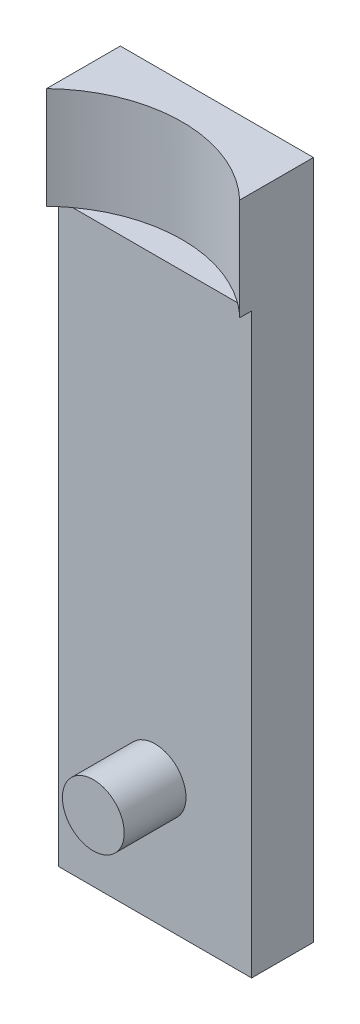
SolidWorks part; units mm, degrees
ref_plane "Front Plane" through (0, 0, 0) normal (0, 0, 1) x (1, 0, 0)
ref_plane "Top Plane" through (0, 0, 0) normal (0, 1, 0) x (1, 0, 0)
ref_plane "Right Plane" through (0, 0, 0) normal (1, 0, 0) x (0, 0, -1)
sketch "Sketch1" plane through (0, 0, 0) normal (0, 0, 1) x (1, 0, 0)
  line L1 (-31.25, 110) -> (31.25, 110)
  line L2 (-31.25, 110) -> (-31.25, -110)
  line L3 (-31.25, -110) -> (31.25, -110)
  line L4 (31.25, 110) -> (31.25, -110)
  line L5 (-31.25, 110) -> (31.25, -110) construction
  line L6 (-31.25, -110) -> (31.25, 110) construction
  point P0 (0, 0)
  dimension "D1" = 220
  dimension "D2" = 62.5
extrude "Boss-Extrude1" add sketch "Sketch1" along normal blind 20
sketch "Sketch2" plane through (0, 0, 20) normal (0, 0, 1) x (1, 0, 0)
  line L1 (-31.25, 110) -> (31.25, 110)
  line L2 (-31.25, 110) -> (-31.25, 77)
  line L3 (-31.25, 77) -> (31.25, 77)
  line L4 (31.25, 110) -> (31.25, 77)
  line L5 (31.25, -110) -> (31.25, 110) construction
  dimension "D1" = 33
  dimension "D2" = 62.5
extrude "Boss-Extrude2" add sketch "Sketch2" along normal blind 5
sketch "Sketch3" plane through (0, 0, 20) normal (0, 0, 1) x (1, 0, 0)
  line L2 (-31.25, -110) -> (31.25, -110) construction
  circle A1 centre (0, -70) radius 10
  dimension "D1" = 40
  dimension "D2" = 20
extrude "Cut-Extrude1" cut sketch "Sketch3" against normal through all
sketch "Sketch4" plane through (0, 110, 0) normal (0, 1, 0) x (1, 0, 0)
  line L0 (31.25, -25) -> (0, -56.25)
  line L1 (31.25, -25) -> (-31.25, -25)
  line L2 (-31.25, -25) -> (0, -56.25)
  line L3 (30.0734, -25) -> (-32.3796, -25)
  circle A0 centre (0, -56.25) radius 45
  line M6 (-31.25, 0) -> (-31.25, -25)
  line M7 (-31.25, -25) -> (31.25, -25)
  line M8 (31.25, -25) -> (31.25, 0)
  dimension "D2" = 90
  dimension "D1" = 45
  dimension "45" = 45
extrude "Cut-Extrude2" cut sketch "Sketch4" against normal blind 33 contours A0 L1 M8 M6 M7
sketch "Sketch5" plane through (0, 0, 20) normal (0, 0, 1) x (1, 0, 0)
  circle A0 centre (0, -70) radius 10
  dimension "D1" = 20
extrude "Boss-Extrude3" add sketch "Sketch5" along normal blind 20 separate body
sketch "Sketch6" plane through (0, 0, 0) normal (0, 0, -1) x (-1, 0, 0)
  line L1 (-9.5794, -72.8696) -> (-13.341, -72.8696)
  line L2 (-9.5794, -72.8696) -> (-9.5794, -69.3452)
  line L3 (-9.5794, -69.3452) -> (-13.341, -69.3452)
  line L4 (-13.341, -72.8696) -> (-13.341, -69.3452)
  circle A0 centre (0, -70) radius 10 construction
extrude "Cut-Extrude3" cut sketch "Sketch6" against normal blind 7
